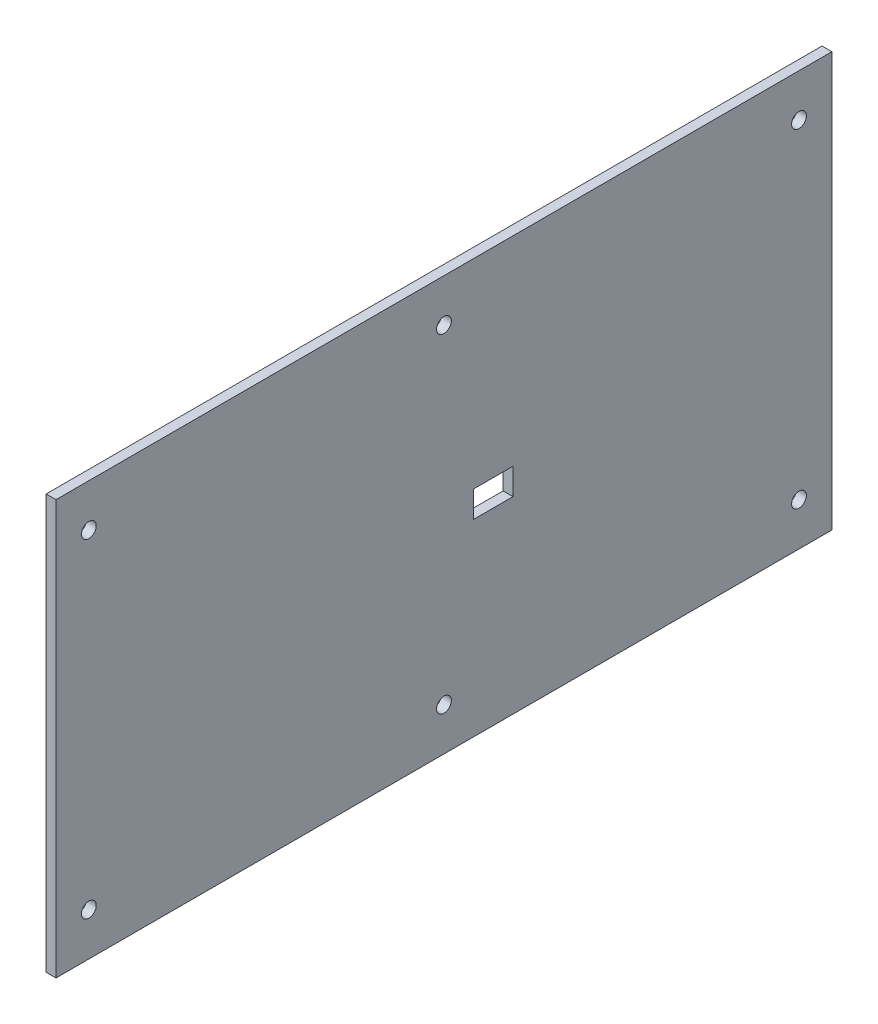
SolidWorks part; units mm, degrees
ref_plane "Спереди" through (0, 0, 0) normal (0, 0, 1) x (1, 0, 0)
ref_plane "Сверху" through (0, 0, 0) normal (0, 1, 0) x (1, 0, 0)
ref_plane "Справа" through (0, 0, 0) normal (1, 0, 0) x (0, 0, -1)
sketch "Эскиз1" plane through (-240, 0, 0) normal (-1, 0, 0) x (0, 0, 1)
  line L1 (0, 123) -> (236, 123)
  line L3 (0, 123) -> (0, -3)
  line L4 (236, 123) -> (236, -3)
  line L5 (0, -3) -> (236, -3)
  line L6 (236, 0) -> (236, 120) construction
  line L7 (0, 120) -> (0, 0) construction
  line L8 (0, 123) -> (236, 123) construction
  line L9 (236, -3) -> (0, -3) construction
extrude "Бобышка-Вытянуть1" add sketch "Эскиз1" along normal blind 3
sketch "Эскиз2" plane through (-243, 0, 0) normal (-1, 0, 0) x (0, 0, 1)
  circle A0 centre (226, 110) radius 2.25 construction
  circle A1 centre (118, 110) radius 2.25 construction
  circle A2 centre (10, 110) radius 2.25 construction
  circle A3 centre (226, 110) radius 2.25
  circle A4 centre (118, 110) radius 2.25
  circle A5 centre (10, 110) radius 2.25
  circle A6 centre (226, 10) radius 2.25 construction
  circle A7 centre (118, 10) radius 2.25 construction
  circle A8 centre (10, 10) radius 2.25 construction
  circle A9 centre (226, 10) radius 2.25
  circle A10 centre (118, 10) radius 2.25
  circle A11 centre (10, 10) radius 2.25
extrude "Вырез-Вытянуть1" cut sketch "Эскиз2" against normal through all
sketch "Эскиз3" plane through (-240, 0, 0) normal (1, 0, 0) x (0, 0, -1)
  line L0 (-106, 57.3) -> (-106, 59.3) construction
  line L1 (-106, 57.3) -> (-106, 59.3) construction
  line L2 (-106, 59.3) -> (-100, 59.3) construction
  line L3 (-106, 59.3) -> (-100, 59.3) construction
  line L4 (-100, 57.3) -> (-106, 57.3) construction
  line L5 (-100, 57.3) -> (-106, 57.3) construction
  line L6 (-100, 59.3) -> (-100, 57.3) construction
  line L7 (-100, 59.3) -> (-100, 57.3) construction
  line L8 (-109, 62.3) -> (-109, 54.3)
  line L9 (-109, 62.3) -> (-97, 62.3)
  line L10 (-109, 54.3) -> (-97, 54.3)
  line L11 (-97, 62.3) -> (-97, 54.3)
  dimension "D1" = 3
  dimension "D2" = 2
  dimension "D3" = 3
  dimension "D4" = 3
  dimension "D5" = 3
extrude "Вырез-Вытянуть2" cut sketch "Эскиз3" against normal through all
